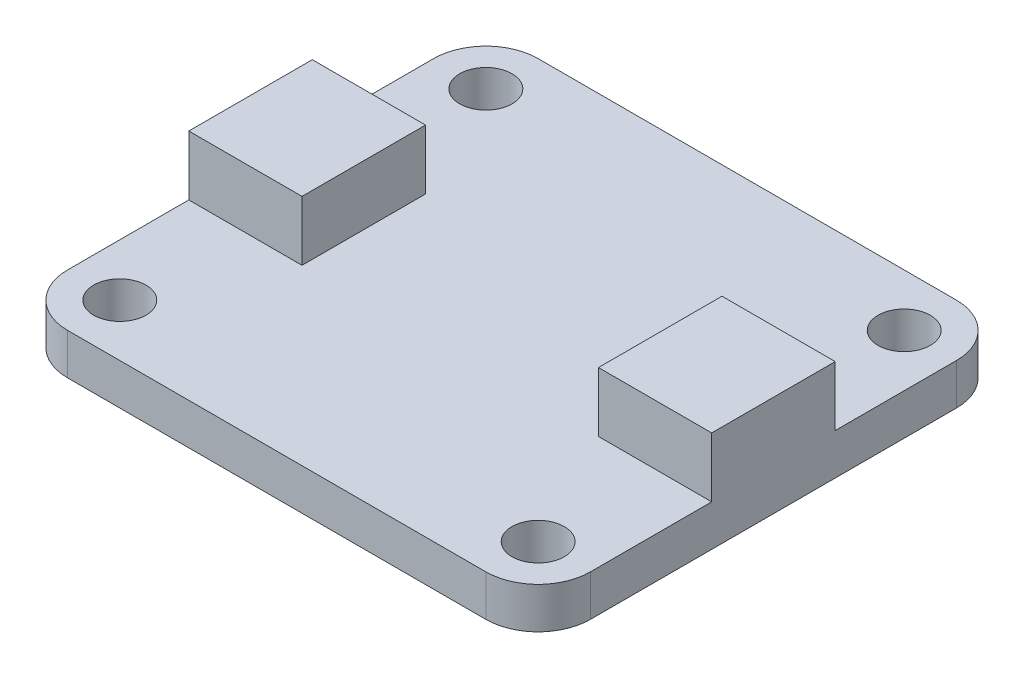
SolidWorks part; units mm, degrees
ref_plane "Front Plane" through (0, 0, 0) normal (0, 0, 1) x (1, 0, 0)
ref_plane "Top Plane" through (0, 0, 0) normal (0, 1, 0) x (1, 0, 0)
ref_plane "Right Plane" through (0, 0, 0) normal (1, 0, 0) x (0, 0, -1)
sketch "Sketch2" plane through (0, 0, 0) normal (0, 1, 0) x (1, 0, 0)
  line L1 (0, 0) -> (25.4, 0)
  line L2 (0, 0) -> (0, 22.86)
  line L3 (0, 22.86) -> (25.4, 22.86)
  line L4 (25.4, 0) -> (25.4, 22.86)
  dimension "D1" = 22.86
  dimension "D2" = 25.4
extrude "Boss-Extrude1" add sketch "Sketch2" along normal blind 2
sketch "Sketch5" plane through (0, 2, 0) normal (0, 1, 0) x (1, 0, 0)
  line L0 (0, 22.86) -> (0, 0) construction
  line L1 (0, 0) -> (25.4, 0) construction
  line L2 (12.7, 22.86) -> (12.7, 0) construction
  line L3 (25.4, 22.86) -> (0, 22.86) construction
  line L4 (0, 11.43) -> (25.4, 11.43) construction
  line L5 (25.4, 0) -> (25.4, 22.86) construction
  circle A0 centre (2.54, 2.54) radius 1.27
  circle A1 centre (22.86, 2.54) radius 1.27
  circle A2 centre (22.86, 20.32) radius 1.27
  circle A3 centre (2.54, 20.32) radius 1.27
  dimension "D3" = 2.54
  dimension "D1" = 2.54
  dimension "D2" = 2.54
extrude "Cut-Extrude1" cut sketch "Sketch5" against normal through all
fillet "Fillet1" radius 2.54 4 edges at (25.4, 1, -22.86) (25.4, 1, 0) (0, 1, 0) (0, 1, -22.86)
sketch "Sketch6" plane through (0, 2, 0) normal (0, 1, 0) x (1, 0, 0)
  line L0 (12.7, 22.86) -> (12.7, 0) construction
  line L1 (22.86, 22.86) -> (2.54, 22.86) construction
  line L2 (2.54, 0) -> (22.86, 0) construction
  line L3 (0, 20.32) -> (0, 2.54) construction
  line L6 (0, 14.43) -> (5.5, 14.43)
  line L7 (0, 14.43) -> (0, 8.43)
  line L8 (0, 8.43) -> (5.5, 8.43)
  line L9 (5.5, 14.43) -> (5.5, 8.43)
  line L10 (25.4, 11.43) -> (0, 11.43) construction
  line L11 (25.4, 2.54) -> (25.4, 20.32) construction
  line L12 (25.4, 14.43) -> (25.4, 8.43)
  line L13 (25.4, 8.43) -> (19.9, 8.43)
  line L14 (19.9, 14.43) -> (19.9, 8.43)
  line L15 (25.4, 14.43) -> (19.9, 14.43)
  point P16 (0, 0)
  point P17 (0, 0)
  point P18 (0, 11.43)
  dimension "D1" = 6
  dimension "D2" = 5.5
extrude "Boss-Extrude2" add sketch "Sketch6" along normal blind 2.9
